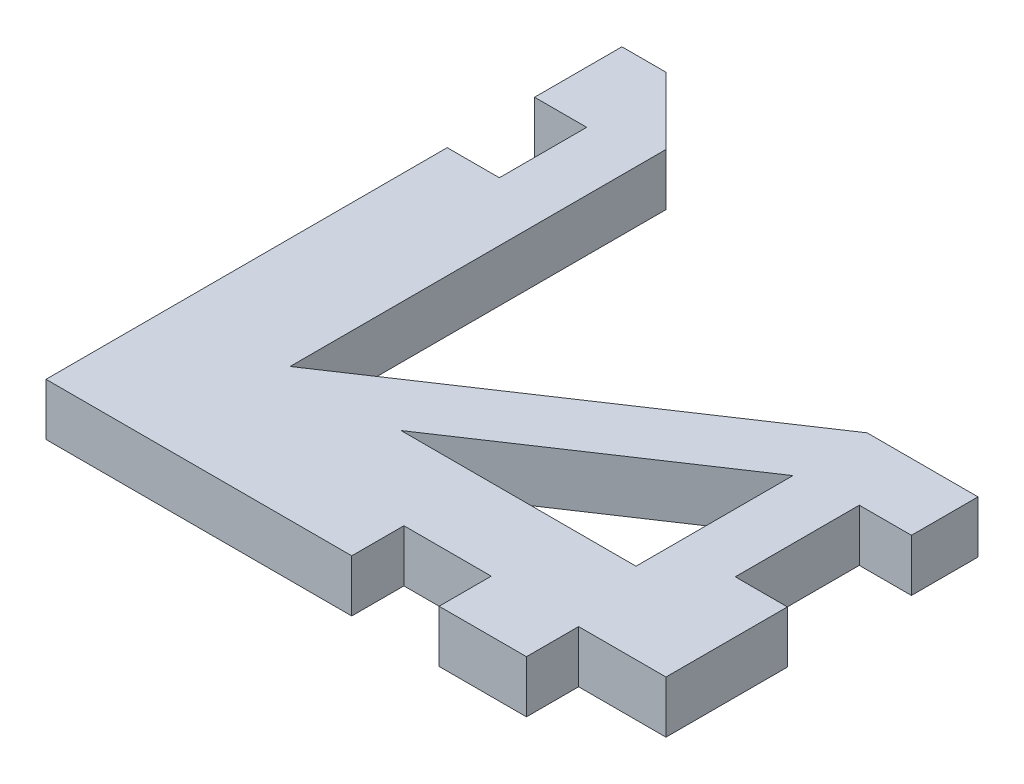
SolidWorks part; units mm, degrees
ref_plane "Front Plane" through (0, 0, 0) normal (0, 0, 1) x (1, 0, 0)
ref_plane "Top Plane" through (0, 0, 0) normal (0, 1, 0) x (1, 0, 0)
ref_plane "Right Plane" through (0, 0, 0) normal (1, 0, 0) x (0, 0, -1)
sketch "Sketch1" plane through (0, 0, 0) normal (0, 1, 0) x (1, 0, 0)
  line L0 (0, 0) -> (-5.969, 0)
  line L1 (-5.969, 0) -> (-5.969, 10)
  line L2 (-5.969, 10) -> (0, 10)
  line L3 (0, 10) -> (0, 20)
  line L4 (0, 20) -> (-5.969, 20)
  line L5 (-5.969, 20) -> (-5.969, 30)
  line L6 (-5.969, 30) -> (-0.928, 30)
  line L7 (-0.928, 30) -> (59.031, -29.959)
  line L8 (59.031, -29.959) -> (49.031, -29.959)
  line L9 (49.031, -29.959) -> (49.031, -35.928)
  line L10 (49.031, -35.928) -> (39.031, -35.928)
  line L11 (39.031, -35.928) -> (39.031, -29.959)
  line L12 (39.031, -29.959) -> (29.959, -29.959)
  line L13 (29.959, -29.959) -> (0, 0)
  dimension "D1" = 5.969
  dimension "D2" = 10
  dimension "D3" = 65
  dimension "D4" = 10
  dimension "D5" = 65.928
  dimension "D6" = 135
extrude "Boss-Extrude1" add sketch "Sketch1" along normal blind 5.969
sketch "Sketch3" plane through (0, 5.969, 0) normal (0, 1, 0) x (1, 0, 0)
  line L0 (6.731, -35.928) -> (29.959, -35.928)
  line L1 (-5.969, 0) -> (6.731, 0)
  line L2 (-5.969, 0) -> (-5.969, -35.928)
  line L3 (-5.969, -35.928) -> (6.731, -35.928)
  line L5 (29.959, -35.928) -> (29.959, -23.228)
  line L7 (6.731, 0) -> (29.959, -23.228)
  line L8 (0, 0) -> (29.959, -29.959) construction
  dimension "D1" = 12.7
  dimension "D2" = 12.7
extrude "Boss-Extrude2" add sketch "Sketch3" against normal blind 5.969
sketch "Sketch4" plane through (0, 5.969, 0) normal (0, 1, 0) x (1, 0, 0)
  line L0 (59.031, -29.959) -> (-0.928, 30) construction
  line L1 (6.731, 22.341) -> (57.531, 22.341)
  line L2 (6.731, 22.341) -> (6.731, -20.688)
  line L3 (6.731, -20.688) -> (57.531, -20.688)
  line L4 (57.531, 22.341) -> (57.531, -20.688)
  line L5 (6.731, 22.341) -> (57.531, -20.688) construction
  line L6 (6.731, -20.688) -> (57.531, 22.341) construction
  line L7 (-5.969, 10) -> (-5.969, -35.928) construction
  line L8 (-5.969, -35.928) -> (29.959, -35.928) construction
  point P4 (32.131, 0.8265)
  dimension "D1" = 12.7
  dimension "D2" = 15.24
  dimension "D3" = 50.8
extrude "Cut-Extrude1" cut sketch "Sketch4" against normal through all
sketch "Sketch5" plane through (0, 5.969, 0) normal (0, 1, 0) x (1, 0, 0)
  line L0 (59.031, -29.959) -> (46.331, -20.688)
  line L1 (46.331, -20.688) -> (46.331, 5.761)
  line L2 (46.331, 5.761) -> (59.031, 5.761)
  line L3 (59.031, 5.761) -> (59.031, -1.859)
  line L4 (59.031, -1.859) -> (53.062, -1.859)
  line L5 (53.062, -1.859) -> (53.062, -16.059)
  line L6 (53.062, -16.059) -> (59.031, -16.059)
  line L7 (59.031, -16.059) -> (59.031, -29.959)
  line L8 (6.731, -20.688) -> (49.76, -20.688) construction
  dimension "D1" = 14.2
  dimension "D2" = 12.7
  dimension "D3" = 5.969
  dimension "D4" = 7.62
  dimension "D5" = 13.9
extrude "Boss-Extrude3" add sketch "Sketch5" against normal up to surface (5.969 mm away) up to face at (19.6171, 0, 9.5637)
sketch "Sketch7" plane through (0, 5.969, 0) normal (0, 1, 0) x (1, 0, 0)
  line L0 (46.331, 5.761) -> (6.731, -20.688)
  line L1 (46.331, -2.7214) -> (19.431, -20.688)
  line L2 (46.331, 5.761) -> (46.331, -20.688) construction
  line L3 (6.731, -20.688) -> (46.331, -20.688) construction
  line L4 (6.731, -20.688) -> (19.431, -20.688)
  line L5 (46.331, 5.761) -> (46.331, -2.7214)
  dimension "D1" = 12.7
extrude "Boss-Extrude5" add sketch "Sketch7" against normal up to surface (5.969 mm away) up to face at (28.6787, 0, 8.126)
sketch "Sketch8" plane through (0, 5.969, 0) normal (0, 1, 0) x (1, 0, 0)
  line L0 (-5.969, -35.928) -> (29.959, -35.928) construction
  line L1 (39.031, -29.959) -> (29.031, -29.959)
  line L2 (39.031, -29.959) -> (39.031, -35.928)
  line L3 (39.031, -35.928) -> (29.031, -35.928)
  line L4 (29.031, -29.959) -> (29.031, -35.928)
  line L5 (39.031, -29.959) -> (29.031, -35.928) construction
  line L6 (39.031, -35.928) -> (29.031, -29.959) construction
  point P4 (34.031, -32.9435)
  dimension "D1" = 10
extrude "Cut-Extrude2" cut sketch "Sketch8" against normal through all
